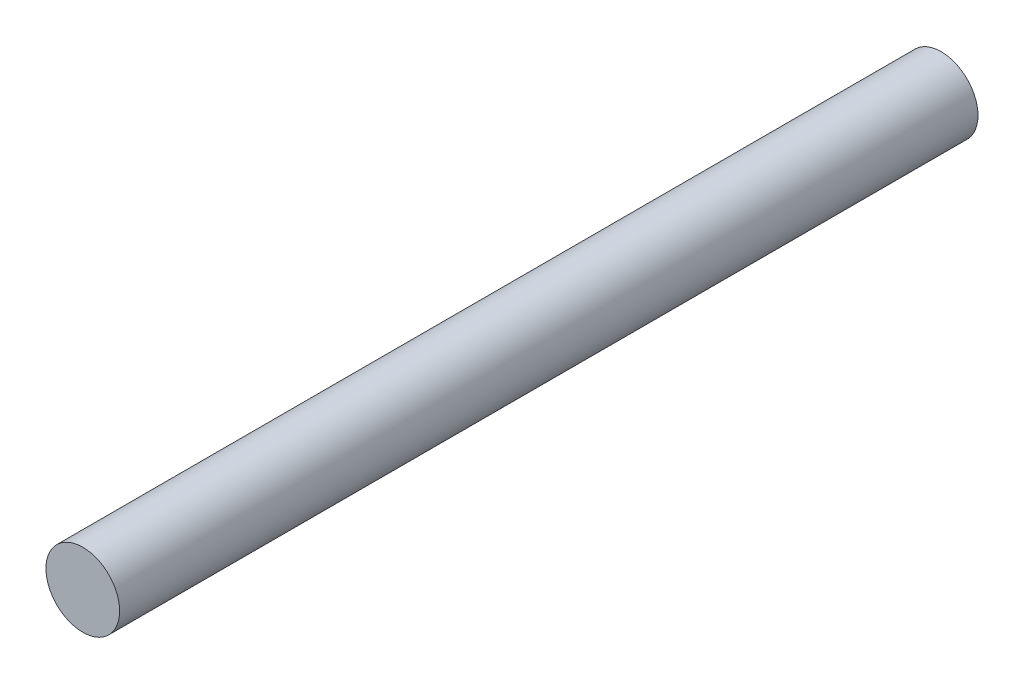
SolidWorks part; units mm, degrees
ref_plane "Front Plane" through (0, 0, 0) normal (0, 0, 1) x (1, 0, 0)
ref_plane "Top Plane" through (0, 0, 0) normal (0, 1, 0) x (1, 0, 0)
ref_plane "Right Plane" through (0, 0, 0) normal (1, 0, 0) x (0, 0, -1)
sketch "Sketch1" plane through (0, 0, 0) normal (0, 0, 1) x (1, 0, 0)
  circle A2 centre (115.6137, 46.338) radius 4.3625
  circle A3 centre (115.6137, 46.338) radius 4.3625
  dimension "D1" = 0.4
extrude "Boss-Extrude1" add sketch "Sketch1" against normal up to surface (101.6 mm away)
